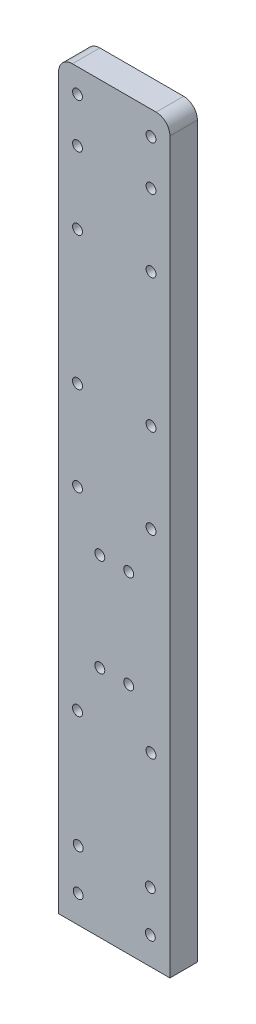
SolidWorks part; units mm, degrees
ref_plane "Front Plane" through (0, 0, 0) normal (0, 0, 1) x (1, 0, 0)
ref_plane "Top Plane" through (0, 0, 0) normal (0, 1, 0) x (1, 0, 0)
ref_plane "Right Plane" through (0, 0, 0) normal (1, 0, 0) x (0, 0, -1)
sketch "Sketch1" plane through (0, 0, 0) normal (0, 0, 1) x (1, 0, 0)
  line L0 (16.2, 0) -> (16.2, 108.14)
  line L1 (16.2, 108.14) -> (0, 108.14)
  line L2 (0, 108.14) -> (0, 0)
  line L3 (0, 0) -> (16.2, 0)
  line L4 (16.2, 57.71) -> (0, 57.71) construction
  line L5 (0, 12.5) -> (16.2, 12.5) construction
  line L6 (0, 24.5) -> (16.2, 24.5) construction
  line L7 (0, 90.16) -> (16.2, 90.16) construction
  line L8 (0, 65.71) -> (16.2, 65.71) construction
  line L9 (8.1, 108.14) -> (8.1, 96.16) construction
  line L11 (0, 96.16) -> (16.2, 96.16) construction
  circle A0 centre (13.45, 55.21) radius 0.72
  circle A1 centre (10.2, 48.21) radius 0.72
  circle A2 centre (13.45, 104.66) radius 0.72
  circle A3 centre (2.75, 98.16) radius 0.72
  circle A4 centre (6, 48.21) radius 0.72
  circle A5 centre (2.75, 27) radius 0.72
  circle A6 centre (2.75, 87.66) radius 0.72
  circle A7 centre (2.75, 55.21) radius 0.72
  circle A8 centre (13.45, 87.66) radius 0.72
  circle A9 centre (13.45, 98.16) radius 0.72
  circle A28 centre (13.45, 68.21) radius 0.72
  circle A29 centre (6, 34) radius 0.72
  circle A32 centre (2.75, 104.66) radius 0.72
  circle A33 centre (10.2, 34) radius 0.72
  circle A34 centre (2.75, 68.21) radius 0.72
  circle A35 centre (13.45, 27) radius 0.72
  circle A36 centre (2.85, 10) radius 0.72
  circle A37 centre (13.35, 10) radius 0.72
  circle A38 centre (13.35, 4) radius 0.72
  circle A39 centre (2.85, 4) radius 0.72
  dimension "D1" = 4
  dimension "D45" = 1.44
  dimension "D2" = 4
  dimension "D3" = 2.85
  dimension "D4" = 2.85
  dimension "D5" = 16.2
  dimension "D6" = 6
  dimension "D7" = 6
  dimension "D8" = 2.85
  dimension "D9" = 2.85
  dimension "D10" = 2.5
  dimension "D11" = 12
  dimension "D12" = 33.21
  dimension "D13" = 2.5
  dimension "D14" = 2.5
  dimension "D15" = 2.75
  dimension "D16" = 2.75
  dimension "D17" = 2.5
  dimension "D18" = 2.5
  dimension "D19" = 2.75
  dimension "D20" = 2.75
  dimension "D21" = 9.5
  dimension "D22" = 6
  dimension "D23" = 9.5
  dimension "D24" = 6
  dimension "D25" = 9.5
  dimension "D26" = 9.5
  dimension "D27" = 6
  dimension "D28" = 6
  dimension "D29" = 8
  dimension "D30" = 24.45
  dimension "D31" = 2.5
  dimension "D32" = 2.5
  dimension "D33" = 2.75
  dimension "D34" = 2.75
  dimension "D35" = 6
  dimension "D36" = 2.75
  dimension "D37" = 2
  dimension "D38" = 2.75
  dimension "D39" = 8.5
  dimension "D40" = 11.98
  dimension "D41" = 2.5
  dimension "D42" = 2.5
  dimension "D43" = 2.75
  dimension "D44" = 2.75
extrude "Boss-Extrude1" add sketch "Sketch1" along normal blind 4
sketch "Sketch2" plane through (0, 0, 0) normal (0, 0, 1) x (1, 0, 0)
  line L0 (16.2, 0) -> (16.2, 108.14) construction
  line L1 (0, 0) -> (16.2, 0)
  line L2 (0, 0) -> (0, 40)
  line L3 (0, 40) -> (16.2, 40)
  line L4 (16.2, 0) -> (16.2, 40)
  dimension "D1" = 40
extrude "Cut-Extrude1" [suppressed] cut sketch "Sketch2" along normal blind 1
fillet "Fillet1" radius 2 2 edges at (16.2, 108.14, 2) (0, 108.14, 2)
sketch "Sketch3" [suppressed] plane through (0, 0, 0) normal (0, 0, 1) x (1, 0, 0)
  line L0 (-74.9273, -47.1892) -> (-74.9273, 60.9508)
  line L1 (-74.9273, 60.9508) -> (-91.1273, 60.9508)
  line L2 (-91.1273, 60.9508) -> (-91.1273, -47.1892)
  line L3 (-91.1273, -47.1892) -> (-74.9273, -47.1892)
  line L4 (-74.9273, 10.5208) -> (-91.1273, 10.5208) construction
  line L5 (-91.1273, -34.6892) -> (-74.9273, -34.6892) construction
  line L6 (-91.1273, -22.6892) -> (-74.9273, -22.6892) construction
  line L7 (-91.1273, 42.9708) -> (-74.9273, 42.9708) construction
  line L8 (-91.1273, 18.5208) -> (-74.9273, 18.5208) construction
  line L9 (-83.0273, 60.9508) -> (-83.0273, 48.9708) construction
  line L10 (-91.1273, 48.9708) -> (-74.9273, 48.9708) construction
  circle A0 centre (-77.6773, 8.0208) radius 0.72
  circle A1 centre (-80.9273, 1.0208) radius 0.72
  circle A2 centre (-77.6773, 57.4708) radius 0.72
  circle A3 centre (-88.3773, 50.9708) radius 0.72
  circle A4 centre (-85.1273, 1.0208) radius 0.72
  circle A5 centre (-88.3773, -20.1892) radius 0.72
  circle A6 centre (-88.3773, 40.4708) radius 0.72
  circle A7 centre (-88.3773, 8.0208) radius 0.72
  circle A8 centre (-77.6773, 40.4708) radius 0.72
  circle A9 centre (-77.6773, 50.9708) radius 0.72
  circle A10 centre (-77.6773, 21.0208) radius 0.72
  circle A11 centre (-85.1273, -13.1892) radius 0.72
  circle A12 centre (-88.3773, 57.4708) radius 0.72
  circle A13 centre (-80.9273, -13.1892) radius 0.72
  circle A14 centre (-88.3773, 21.0208) radius 0.72
  circle A15 centre (-77.6773, -20.1892) radius 0.72
  circle A16 centre (-88.2773, -37.1892) radius 0.72
  circle A17 centre (-77.7773, -37.1892) radius 0.72
  circle A18 centre (-77.7773, -43.1892) radius 0.72
  circle A19 centre (-88.2773, -43.1892) radius 0.72
  dimension "D45" = 1.44
  dimension "D1" = 4
  dimension "D2" = 4
  dimension "D3" = 2.85
  dimension "D4" = 2.85
  dimension "D5" = 16.2
  dimension "D6" = 6
  dimension "D7" = 6
  dimension "D8" = 2.85
  dimension "D9" = 2.85
  dimension "D10" = 2.5
  dimension "D11" = 12
  dimension "D12" = 33.21
  dimension "D13" = 2.5
  dimension "D14" = 2.5
  dimension "D15" = 2.75
  dimension "D16" = 2.75
  dimension "D17" = 2.5
  dimension "D18" = 2.5
  dimension "D19" = 2.75
  dimension "D20" = 2.75
  dimension "D21" = 9.5
  dimension "D22" = 6
  dimension "D23" = 9.5
  dimension "D24" = 6
  dimension "D25" = 9.5
  dimension "D26" = 9.5
  dimension "D27" = 6
  dimension "D28" = 6
  dimension "D29" = 8
  dimension "D30" = 24.45
  dimension "D31" = 2.5
  dimension "D32" = 2.5
  dimension "D33" = 2.75
  dimension "D34" = 2.75
  dimension "D35" = 6
  dimension "D36" = 2.75
  dimension "D37" = 2
  dimension "D38" = 2.75
  dimension "D39" = 8.5
  dimension "D40" = 11.98
  dimension "D41" = 2.5
  dimension "D42" = 2.5
  dimension "D43" = 2.75
  dimension "D44" = 2.75
